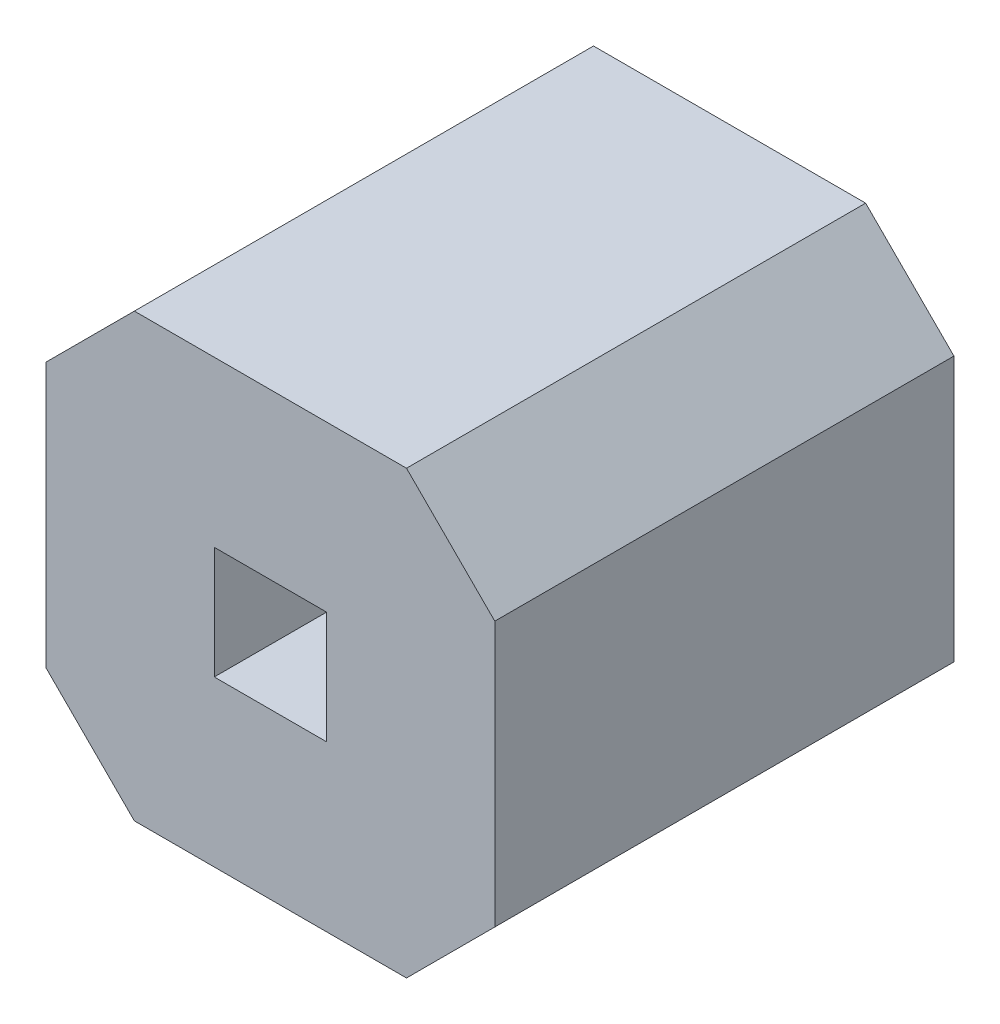
SolidWorks part; units mm, degrees
ref_plane "Alzado" through (0, 0, 0) normal (0, 0, 1) x (1, 0, 0)
ref_plane "Planta" through (0, 0, 0) normal (0, 1, 0) x (1, 0, 0)
ref_plane "Vista lateral" through (0, 0, 0) normal (1, 0, 0) x (0, 0, -1)
sketch "Croquis1" plane through (0, 0, 0) normal (0, 0, 1) x (1, 0, 0)
  line L0 (0.9525, -0.932) -> (0, -0.932) construction
  line L1 (0, 0) -> (2.541, 0)
  line L2 (0, 0) -> (0, -2.5)
  line L3 (0, -2.5) -> (2.541, -2.5)
  line L4 (1.5885, -1.568) -> (2.541, -1.568) construction
  line L5 (0, 0) -> (1, 0) construction
  line L6 (2.541, 0) -> (2.541, -2.5)
  line L7 (0.9525, -1.25) -> (0.9525, -0.932) construction
  line L8 (1, 0) -> (1.636, 0) construction
  line L10 (1.5885, -1.25) -> (1.5885, -1.568) construction
  line L12 (0.9525, -0.932) -> (1.5885, -0.932)
  line L13 (0.9525, -0.932) -> (0.9525, -1.568)
  line L14 (0.9525, -1.568) -> (1.5885, -1.568)
  line L15 (1.5885, -0.932) -> (1.5885, -1.568)
  dimension "D1" = 0.318
  dimension "D2" = 0.9525
extrude "Saliente-Extruir2" add sketch "Croquis1" along normal blind 2.6
chamfer "Chaflán2" distance 0.5 angle 45 4 edges at (2.541, -2.5, 1.3) (2.541, 0, 1.3) (0, -2.5, 1.3) (0, 0, 1.3)
